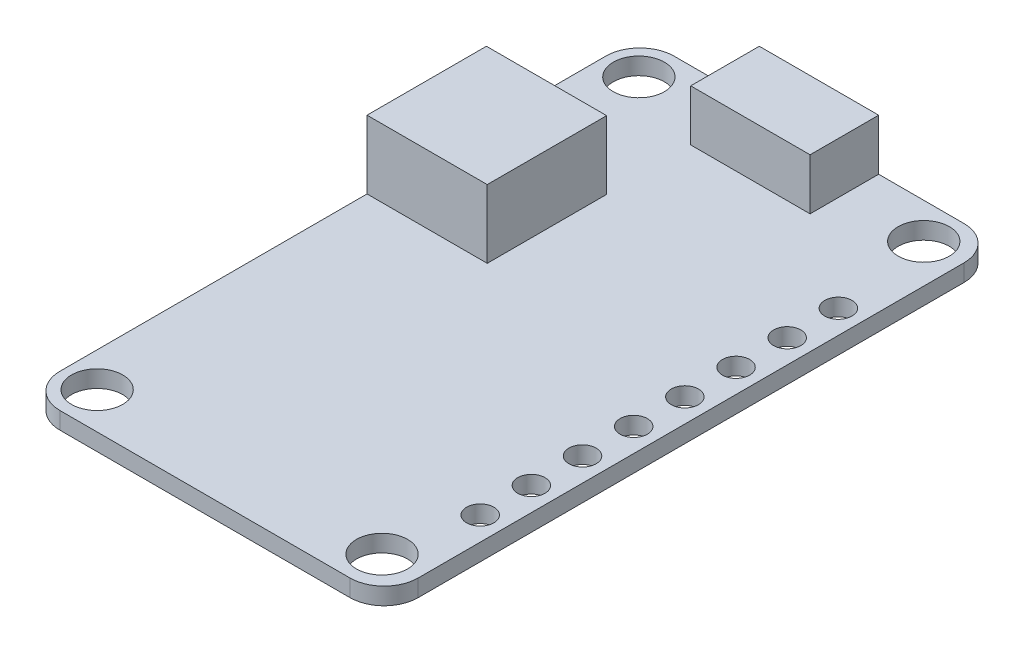
SolidWorks part; units mm, degrees
ref_plane "Alzado" through (0, 0, 0) normal (0, 0, 1) x (1, 0, 0)
ref_plane "Planta" through (0, 0, 0) normal (0, 1, 0) x (1, 0, 0)
ref_plane "Vista lateral" through (0, 0, 0) normal (1, 0, 0) x (0, 0, -1)
sketch "Croquis1" plane through (0, 0, 0) normal (0, 1, 0) x (1, 0, 0)
  line L1 (10.5, -18) -> (-10.5, -18)
  line L2 (10.5, -18) -> (10.5, 18)
  line L3 (10.5, 18) -> (-10.5, 18)
  line L4 (-10.5, -18) -> (-10.5, 18)
  line L5 (10.5, -18) -> (-10.5, 18) construction
  line L6 (10.5, 18) -> (-10.5, -18) construction
  point P0 (0, 0)
  dimension "D1" = 21
  dimension "D2" = 36
extrude "Saliente-Extruir1" add sketch "Croquis1" along normal blind 5
sketch "Croquis2" plane through (0, 5, 0) normal (0, 1, 0) x (1, 0, 0)
  line L0 (-10.5, 18) -> (-16.4739, 18) construction
  line L1 (-10.5, 9) -> (-16.4739, 9) construction
  line L2 (-10.5, 18) -> (-10.5, -18) construction
  line L5 (-10.5, 9) -> (-3.4519, 9)
  line L6 (-10.5, 9) -> (-10.5, 2)
  line L7 (-10.5, 2) -> (-3.4519, 2)
  line L8 (-3.4519, 9) -> (-3.4519, 2)
  dimension "D1" = 9
  dimension "D3" = 7.0481
  dimension "D4" = 7
extrude "Cortar-Extruir1" cut sketch "Croquis2" against normal blind 4 and the other way blind 7 flip side to cut
sketch "Croquis3" plane through (0, 1, 0) normal (0, 1, 0) x (1, 0, 0)
  line L0 (10.5, 18) -> (-10.5, 18) construction
  line L1 (-3.5, 18) -> (3.5, 18)
  line L2 (-3.5, 18) -> (-3.5, 13.9777)
  line L3 (-3.5, 13.9777) -> (3.5, 13.9777)
  line L4 (3.5, 18) -> (3.5, 13.9777)
  line L6 (10.5, -18) -> (10.5, 18) construction
  dimension "D1" = 7
extrude "Saliente-Extruir2" add sketch "Croquis3" along normal blind 3
sketch "Croquis4" plane through (0, 0, -18) normal (0, 0, -1) x (-1, 0, 0)
  line L1 (-2.7256, 3.2987) -> (2.9538, 3.2987)
  line L2 (-2.7256, 3.2987) -> (-2.7256, 1.321)
  line L3 (-2.7256, 1.321) -> (2.9538, 1.321)
  line L4 (2.9538, 3.2987) -> (2.9538, 1.321)
extrude "Cortar-Extruir2" cut sketch "Croquis4" against normal blind 3
sketch "Croquis5" plane through (-10.5, 0, 0) normal (-1, 0, 0) x (0, 0, 1)
  line L1 (-8.306, 4.3219) -> (-2.6288, 4.3219)
  line L2 (-8.306, 4.3219) -> (-8.306, 1.3755)
  line L3 (-8.306, 1.3755) -> (-2.6288, 1.3755)
  line L4 (-2.6288, 4.3219) -> (-2.6288, 1.3755)
extrude "Cortar-Extruir3" cut sketch "Croquis5" against normal blind 6
fillet "Redondeo1" radius 2 4 edges at (10.5, 0.5, 18) (10.5, 0.5, -18) (-10.5, 0.5, 18) (-10.5, 0.5, -18)
sketch "Croquis7" plane through (0, 1, 0) normal (0, 1, 0) x (1, 0, 0)
  circle A0 centre (-8.4746, 15.9122) radius 1.5
extrude "Cortar-Extruir4" cut sketch "Croquis7" against normal blind 10
sketch "Croquis8" plane through (0, 1, 0) normal (0, 1, 0) x (1, 0, 0)
  line L0 (-8.4746, 15.9122) -> (8.2311, 15.9122) construction
  line L1 (-8.4746, 15.9122) -> (-8.4746, -15.8507) construction
  line L2 (8.2311, 15.9122) -> (8.2311, -15.8507) construction
  circle A0 centre (8.2311, 15.9122) radius 1.5
  circle A1 centre (-8.4746, -15.8507) radius 1.5
  circle A2 centre (8.2311, -15.8507) radius 1.5
extrude "Cortar-Extruir5" cut sketch "Croquis8" against normal blind 10
sketch "Croquis9" plane through (0, 1, 0) normal (0, 1, 0) x (1, 0, 0)
  line L0 (5.9763, 13.4614) -> (14.1054, 13.4614) construction
  line L1 (6.5103, -12.5872) -> (13.4527, -12.5872) construction
  circle A0 centre (9.1211, -10.9852) radius 0.7983
extrude "Cortar-Extruir6" cut sketch "Croquis9" against normal blind 10
pattern_linear "MatrizL1" count 8 spacing 3 along (0, 0, -1) of "Cortar-Extruir6"
